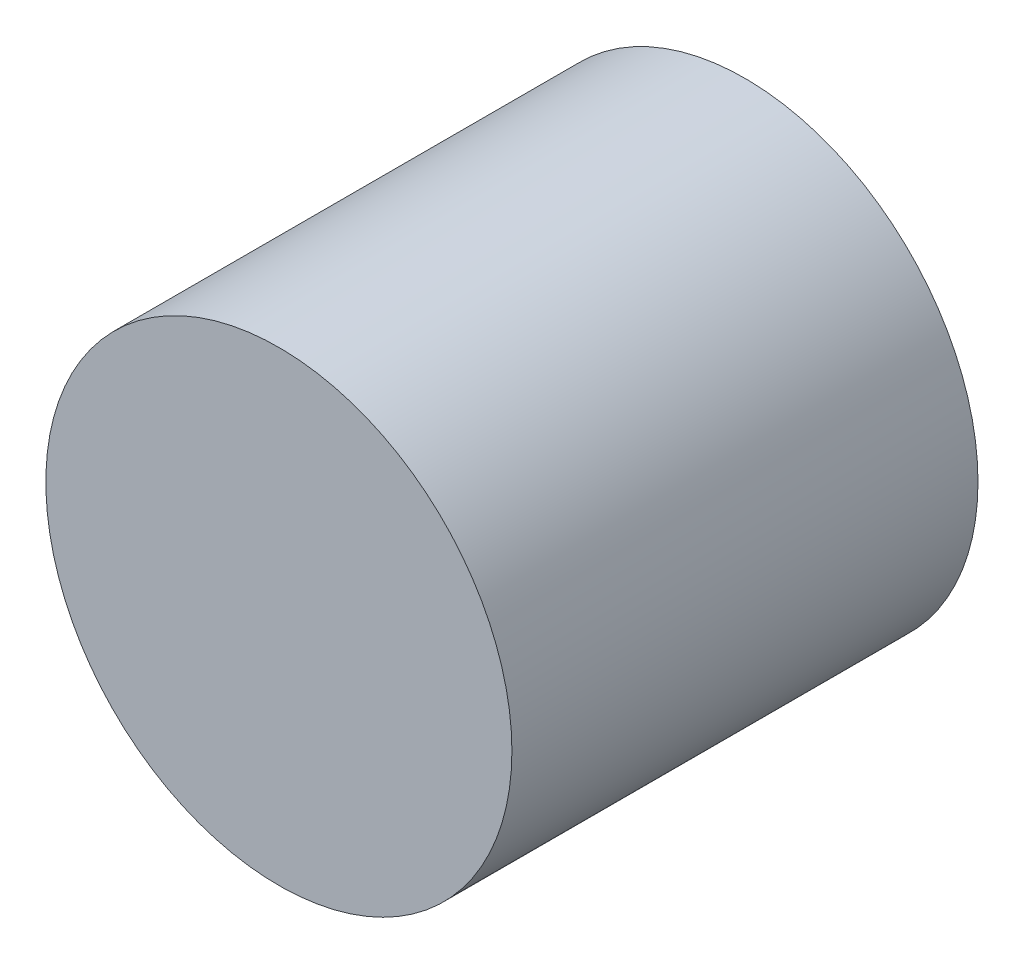
SolidWorks part; units mm, degrees
ref_plane "前视基准面" through (0, 0, 0) normal (0, 0, 1) x (1, 0, 0)
ref_plane "上视基准面" through (0, 0, 0) normal (0, 1, 0) x (1, 0, 0)
ref_plane "右视基准面" through (0, 0, 0) normal (1, 0, 0) x (0, 0, -1)
sketch "草图1" plane through (0, 0, 0) normal (0, 0, 1) x (1, 0, 0)
  circle A0 centre (-7.2124, 6.5907) radius 5
  dimension "D1" = 10
extrude "凸台-拉伸1" add sketch "草图1" along normal blind 10
